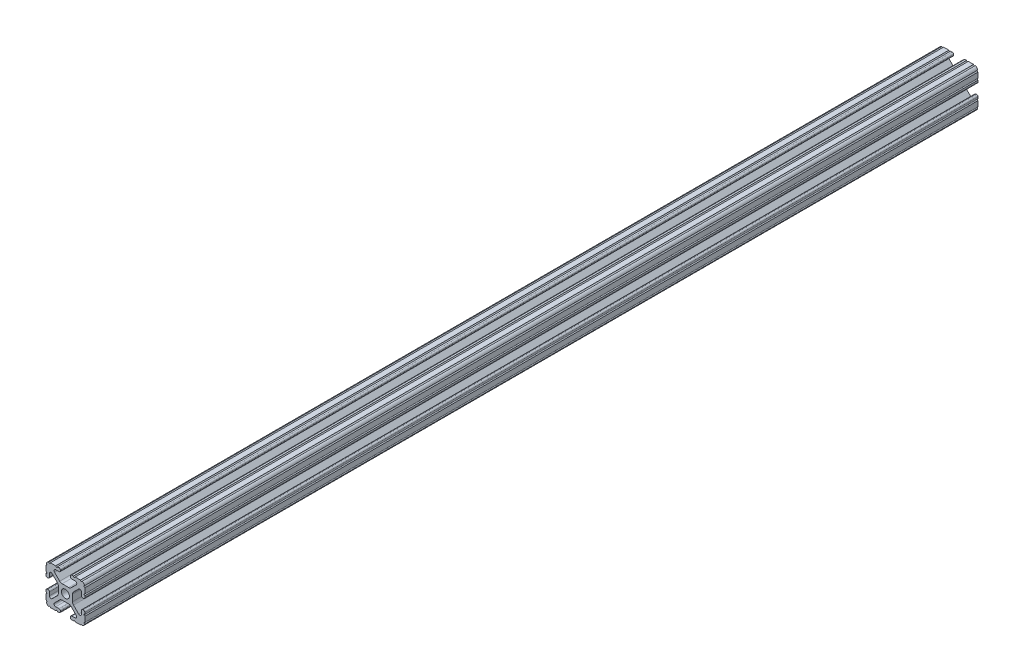
SolidWorks part; units mm, degrees
ref_plane "Front Plane" through (0, 0, 0) normal (0, 0, 1) x (1, 0, 0)
ref_plane "Top Plane" through (0, 0, 0) normal (0, 1, 0) x (1, 0, 0)
ref_plane "Right Plane" through (0, 0, 0) normal (1, 0, 0) x (0, 0, -1)
sketch "Sketch2" plane through (0, 0, 0) normal (0, 0, 1) x (1, 0, 0)
  line L0 (0, 12.7) -> (0, -12.7) construction
  line L1 (-12.7, 0) -> (12.7, 0) construction
  line L2 (3.2512, -12.7) -> (12.7, -12.7)
  line L3 (12.7, -12.7) -> (12.7, -3.2512)
  line L4 (3.2512, -12.7) -> (3.2512, -10.4902)
  line L5 (3.2512, -10.4902) -> (8.9276, -10.4902)
  line L6 (8.9276, -10.4902) -> (3.0856, -4.6482)
  line L7 (0, 0) -> (12.7, -12.7) construction
  line L8 (12.7, -3.2512) -> (10.4902, -3.2512)
  line L9 (10.4902, -3.2512) -> (10.4902, -8.9276)
  line L10 (10.4902, -8.9276) -> (4.6482, -3.0856)
  circle A0 centre (0, 0) radius 2.6035
  arc A1 (6.3485, -10.4902) -> (7.1039, -8.6665) centre (6.3485, -9.4219) ccw construction
  point P8 (0, -4.6482)
  dimension "Center Hole Diameter" = 5.207
  dimension "Rail Height" = 25.4
  dimension "Rail Width" = 25.4
  dimension "T-Slot Width" = 6.5024
  dimension "Slot Inner Width" = 14.8336
  dimension "Thickness" = 2.2098
  dimension "Slot Depth" = 5.842
  dimension "D1" = 2.2098
sketch "Sketch3" plane through (0, 0, 0) normal (1, 0, 0) x (0, 0, -1)
  line L0 (-304.8, -12.7) -> (304.8, -12.7) construction
  line L1 (-279.4, 0) -> (279.4, 0) construction
  dimension "Length" = 609.6
  dimension "D1" = 25.4
sketch "Sketch4" plane through (0, 0, 0) normal (0, 0, 1) x (1, 0, 0)
  line L0 (4.1904, -12.7) -> (10.1173, -12.7)
  line L1 (3.2512, -12.7) -> (12.7, -12.7) construction
  line L2 (3.2512, -12.7) -> (3.2512, -10.4902) construction
  line L3 (3.2512, -10.4902) -> (8.9276, -10.4902) construction
  line L4 (3.2512, -11.4294) -> (3.2512, -11.7608)
  line L5 (4.1904, -10.4902) -> (6.3485, -10.4902)
  line L6 (0, -4.6482) -> (2.164, -4.6482)
  line L7 (8.9276, -10.4902) -> (3.0856, -4.6482) construction
  line L8 (3.7373, -5.2999) -> (7.1039, -8.6665)
  line L9 (12.7, -12.7) -> (12.7, -3.2512) construction
  line L10 (10.4902, -8.9276) -> (4.6482, -3.0856) construction
  line L11 (10.4902, -3.2512) -> (10.4902, -8.9276) construction
  line L12 (10.4902, -6.3485) -> (10.4902, -4.1904)
  line L13 (12.7, -3.2512) -> (10.4902, -3.2512) construction
  line L14 (11.4294, -3.2512) -> (11.7608, -3.2512)
  line L15 (12.7, -4.1904) -> (12.7, -10.1173)
  line L16 (8.6665, -7.1039) -> (5.2999, -3.7373)
  line L17 (4.6482, 0) -> (4.6482, -2.164)
  line L18 (-12.7, 0) -> (12.7, 0) construction
  line L19 (0, -4.6482) -> (0, -2.6035)
  line L20 (0, 12.7) -> (0, -12.7) construction
  line L21 (4.6482, 0) -> (2.6035, 0)
  arc A0 (3.2512, -11.7608) -> (4.1904, -12.7) centre (4.1904, -11.7608) ccw
  arc A2 (3.2512, -11.4294) -> (4.1904, -10.4902) centre (4.1904, -11.4294) cw
  arc A3 (6.3485, -10.4902) -> (7.1039, -8.6665) centre (6.3485, -9.4219) ccw
  arc A4 (2.164, -4.6482) -> (3.7373, -5.2999) centre (2.164, -6.8732) cw
  arc A5 (10.1173, -12.7) -> (12.7, -10.1173) centre (10.1173, -10.1173) ccw
  arc A6 (8.6665, -7.1039) -> (10.4902, -6.3485) centre (9.4219, -6.3485) ccw
  arc A7 (10.4902, -4.1904) -> (11.4294, -3.2512) centre (11.4294, -4.1904) cw
  arc A8 (11.7608, -3.2512) -> (12.7, -4.1904) centre (11.7608, -4.1904) cw
  arc A9 (5.2999, -3.7373) -> (4.6482, -2.164) centre (6.8732, -2.164) cw
  circle A10 centre (0, 0) radius 2.6035 construction
  arc A11 (0, -2.6035) -> (2.6035, 0) centre (0, 0) ccw
  dimension "D1" = 2.5827
  dimension "D2" = 2.225
  dimension "D3" = 0.9392
extrude "Boss-Extrude1" add sketch "Sketch4" along normal mid plane 609.6
sketch "Sketch5" plane through (0, 0, 0) normal (0, 0, 1) x (1, 0, 0)
  line L0 (3.2512, -12.7) -> (12.7, -12.7) construction
  line L1 (4.1904, -10.4902) -> (6.3485, -10.4902) construction
  line L3 (0, 0) -> (12.7, -12.7) construction
  line L4 (6.3485, -10.4902) -> (6.3485, -12.7) construction
  line L5 (8.9276, -10.4902) -> (3.0856, -4.6482) construction
  circle A0 centre (10.3562, -12.7) radius 0.5524
  circle A1 centre (5.796, -12.7) radius 0.5524
  circle A2 centre (12.7, -10.3562) radius 0.5524
  circle A3 centre (12.7, -5.796) radius 0.5524
  point P10 (5.2694, -10.4902)
  point P12 (9.4219, -6.3485)
  dimension "D1" = 1.1049
extrude "Cut-Extrude1" cut sketch "Sketch5" against normal through all both and the other way through all
mirror "Mirror1" about plane through (0, 0, 0) normal (1, 0, 0) of bodies 137 134
mirror "Mirror2" about plane through (0, 0, 0) normal (0, 1, 0) of bodies 135
sketch "Sketch6" plane through (0, 0, 0) normal (0, 1, 0) x (1, 0, 0)
  line L1 (-15.935, -304.8) -> (15.815, -304.8)
  line L2 (-15.935, -304.8) -> (-15.935, -279.4)
  line L3 (-15.935, -279.4) -> (15.815, -279.4)
  line L4 (15.815, -304.8) -> (15.815, -279.4)
  line L5 (-12.7, -284.492) -> (12.58, -284.492) construction
  line L6 (-12.7, -304.8) -> (-12.7, 304.8) construction
  line L7 (12.58, 304.8) -> (12.58, -304.8) construction
  point P11 (-0.06, -284.492)
  point P12 (-0.06, -304.8)
  dimension "D1" = 25.4
  dimension "D2" = 31.75
extrude "Cut-Extrude2" cut sketch "Sketch6" against normal mid plane 25.4
equation "\"D1@Boss-Extrude1\"=\"Length@Sketch3\""
equation "\"D1@Sketch2\"=\"Thickness@Sketch2\""
equation "\"D2@Sketch4\"=\"Slot Inner Width@Sketch2\"*0.15"
equation "\"D1@Sketch4\"=\"D3@Sketch4\"*2.75"
equation "\"D3@Sketch4\"=\"Thickness@Sketch2\"*0.425"
equation "\"D1@Sketch5\"=\"Thickness@Sketch2\"*0.5"
